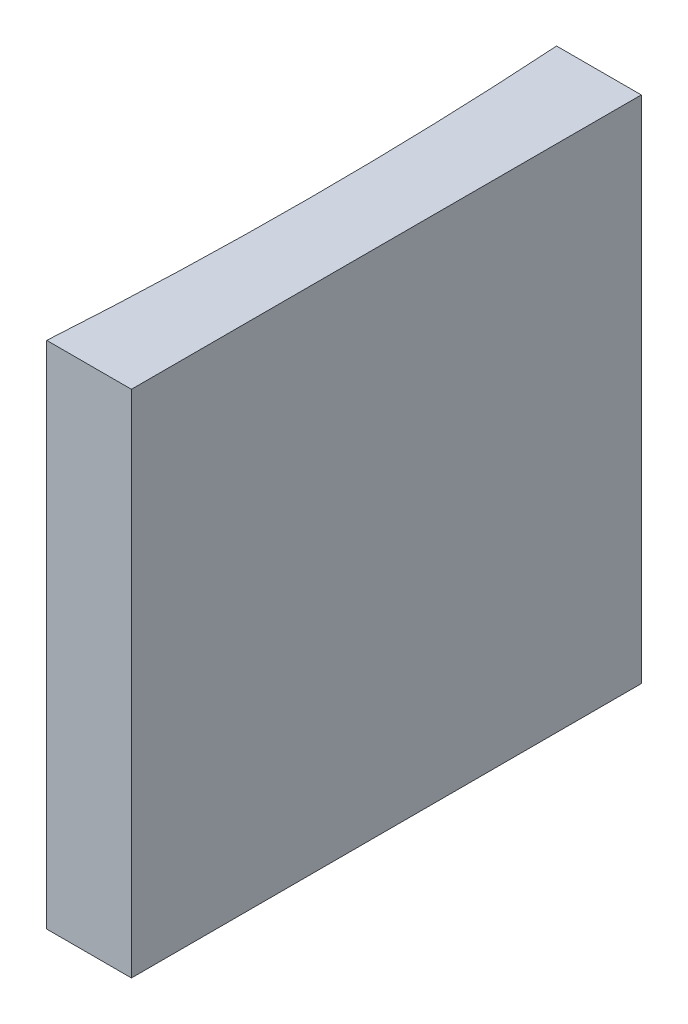
SolidWorks part; units mm, degrees
ref_plane "前视基准面" through (0, 0, 0) normal (0, 0, 1) x (1, 0, 0)
ref_plane "上视基准面" through (0, 0, 0) normal (0, 1, 0) x (1, 0, 0)
ref_plane "右视基准面" through (0, 0, 0) normal (1, 0, 0) x (0, 0, -1)
sketch "草图1" plane through (0, 0, 0) normal (0, 1, 0) x (1, 0, 0)
  line L0 (0, 0) -> (0, -20)
  line L1 (0, 0) -> (-3.3227, 0)
  line L2 (0, -20) -> (-3.3227, -20)
  line L3 (8.2336, -10) -> (-10.4405, -10) construction
  arc A0 (-3.3227, -20) -> (-3.3227, 0) centre (-158.1, -10) ccw
  point P7 (-3, -10)
  point P8 (0, -10)
  dimension "D2" = 155.1
  dimension "D3" = 3
  dimension "D1" = 20
extrude "凸台-拉伸1" add sketch "草图1" along normal blind 20
